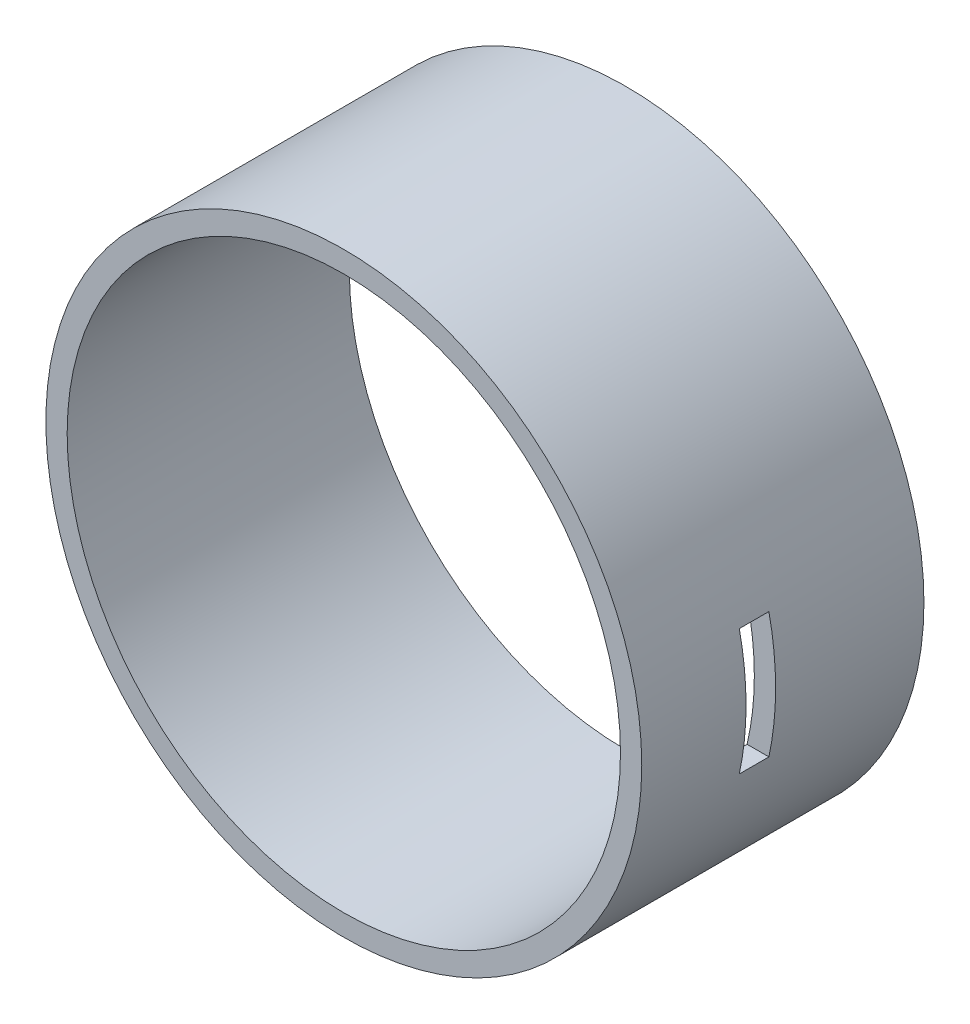
SolidWorks part; units mm, degrees
material "6061-T6 (SS)"
ref_plane "Front" through (0, 0, 0) normal (0, 0, 1) x (1, 0, 0)
ref_plane "Top" through (0, 0, 0) normal (0, 1, 0) x (1, 0, 0)
ref_plane "Right" through (0, 0, 0) normal (1, 0, 0) x (0, 0, -1)
sketch "Sketch1" plane through (0, 0, 0) normal (0, 0, 1) x (1, 0, 0)
  circle A0 centre (0, 0) radius 140
  circle A1 centre (0, 0) radius 130
extrude "Boss-Extrude1" add sketch "Sketch1" along normal blind 132.6 contours A1 | A0
hole_wizard "M4x0.7 Tapped Hole1" positions "Sketch3" profile "Sketch4" tap size "M4x0.7" standard "ANSI Metric"
sketch "Sketch3" plane through (0, 0, 0) normal (0, 0, -1) x (-1, 0, 0)
  point P0 (0, 135)
  point P1 (135, 0)
  point P3 (95.5, 95.5)
  point P5 (95.5, -95.5)
  point P9 (0, -135)
  point P11 (-95.5, -95.5)
  point P13 (-135, 0)
  point P15 (-95.5, 95.5)
cosmetic thread "Hole Thread10" parameters "D1"=18, "D2"=4
cosmetic thread "Hole Thread11" parameters "D1"=18, "D2"=4
cosmetic thread "Hole Thread12" parameters "D1"=18, "D2"=4
cosmetic thread "Hole Thread13" parameters "D1"=18, "D2"=4
cosmetic thread "Hole Thread14" parameters "D1"=18, "D2"=4
cosmetic thread "Hole Thread15" parameters "D1"=18, "D2"=4
cosmetic thread "Hole Thread16" parameters "D1"=18, "D2"=4
cosmetic thread "Hole Thread17" parameters "D1"=18, "D2"=4
sketch "Sketch4" plane through (0, 135, 0) normal (1, 0, 0) x (0, 1, 0)
  line L0 (0, 0) -> (0, 20.9914)
  line L1 (0, 20.9914) -> (1.65, 20)
  line L2 (1.65, 20) -> (1.65, 0)
  line L5 (1.65, 0) -> (0, 0)
  line L10 (0, 20.9914) -> (-1.65, 20) construction
  line L11 (0, -6.35) -> (0, 107.95) construction
  dimension "Tap Drill Dia." = 3.3
  dimension "Tap Drill Depth" = 20
  dimension "Drill Angle" = 118
sketch "Sketch5" plane through (0, 0, 0) normal (1, 0, 0) x (0, 0, -1)
  line L1 (-69.7, 29.575) -> (-83.6, 29.575)
  line L2 (-69.7, 29.575) -> (-69.7, -29.575)
  line L3 (-69.7, -29.575) -> (-83.6, -29.575)
  line L4 (-83.6, 29.575) -> (-83.6, -29.575)
  point P4 (0, 0)
  point P5 (0, 0)
  point P6 (0, 0)
  point P7 (0, 0)
  point P8 (0, 0)
  point P9 (0, 0)
  point P10 (0, 0)
  point P11 (0, 0)
  point P12 (0, 0)
  point P13 (0, 0)
extrude "Cut-Extrude1" cut sketch "Sketch5" along normal blind 140
